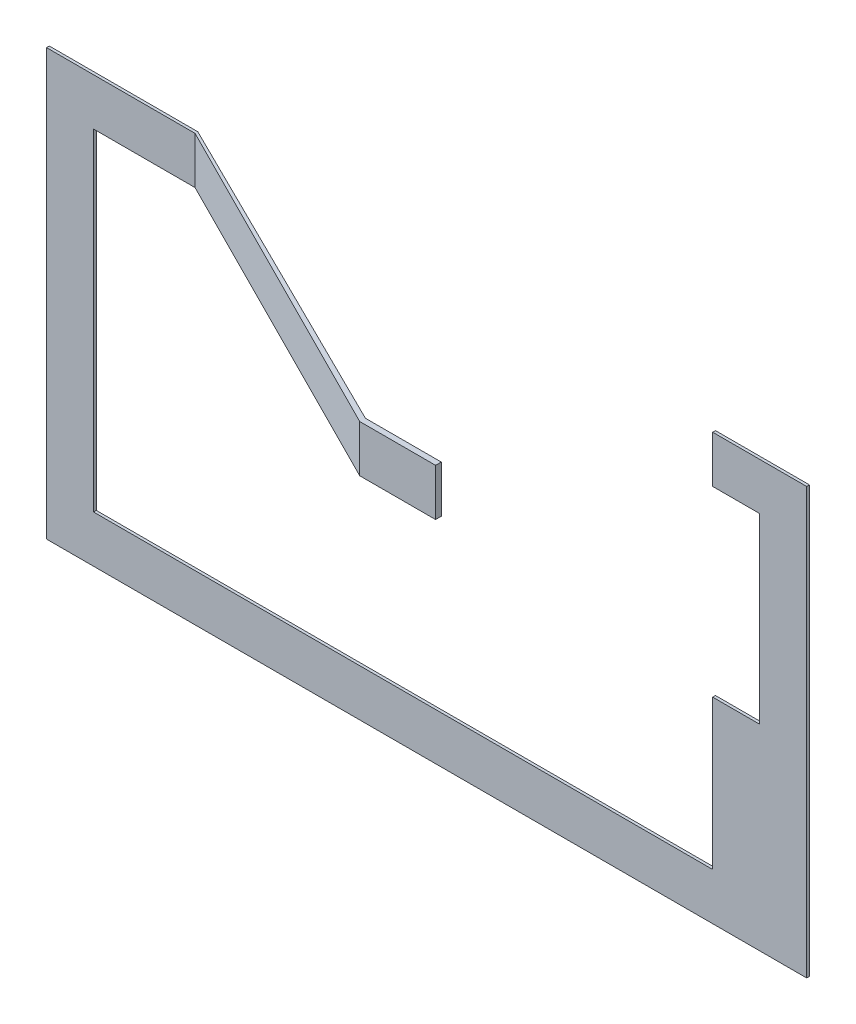
SolidWorks part; units mm, degrees
ref_plane "Front Plane" through (0, 0, 0) normal (0, 0, 1) x (1, 0, 0)
ref_plane "Top Plane" through (0, 0, 0) normal (0, 1, 0) x (1, 0, 0)
ref_plane "Right Plane" through (0, 0, 0) normal (1, 0, 0) x (0, 0, -1)
sketch "Sketch1" plane through (0, 0, 0) normal (0, 0, 1) x (1, 0, 0)
  line L0 (-9214.464, 6700) -> (-9214.464, 5850)
  line L1 (1000, 6700) -> (-11900, 6700) construction
  line L2 (-4900, 5850) -> (-11050, 5850) construction
  line L3 (-9214.464, 5850) -> (-11050, 5850)
  line L4 (-11050, 5850) -> (-11050, -150)
  line L5 (-11050, -150) -> (150, -150)
  line L6 (150, -150) -> (150, 2550)
  line L7 (150, 2550) -> (1000, 2550)
  line L8 (1000, 5850) -> (1000, -150) construction
  line L9 (3650, 2550) -> (150, 2550) construction
  line L10 (1000, 2550) -> (1000, 5850)
  line L11 (1000, 5850) -> (150, 5850)
  line L12 (150, 5850) -> (150, 6700)
  line L13 (150, 6700) -> (1850, 6700)
  line L14 (1000, 6700) -> (6499.448, 6700) construction
  line L15 (1850, 6700) -> (1850, -1000)
  line L16 (1850, -1000) -> (-11900, -1000)
  line L17 (-11900, -1000) -> (-11900, 6700)
  line L18 (-11900, 6700) -> (-9214.464, 6700)
  line L20 (1000, -1000) -> (1000, -150) construction
  dimension "D1" = 850
extrude "Extrude1" add sketch "Sketch1" against normal blind 50
sketch "Sketch2" plane through (0, 6700, 0) normal (0, 1, 0) x (1, 0, 0)
  line L0 (-9214.464, 0) -> (-3210.1391, -3025)
  line L1 (-4900, -3025) -> (150, -3025) construction
  line L2 (-3210.1391, -3025) -> (-1837.6985, -3025)
  line L3 (-1837.6985, -3025) -> (-1837.6985, -2922.0618)
  line L4 (-1837.6985, -2922.0618) -> (-3210.1391, -2922.0618)
  line L5 (-3210.1391, -2922.0618) -> (-9214.464, 50)
  line L6 (-9214.464, 50) -> (-9214.464, 0)
extrude "Extrude2" add sketch "Sketch2" against normal blind 850
